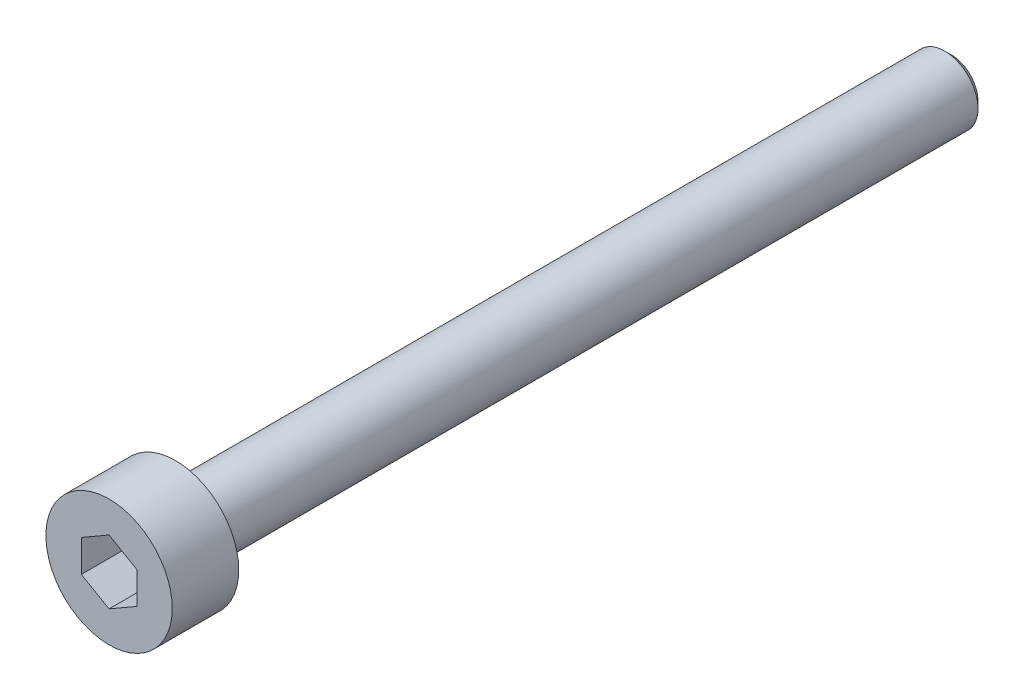
SolidWorks part; units mm, degrees
ref_plane "Front Plane" through (0, 0, 0) normal (0, 0, 1) x (1, 0, 0)
ref_plane "Top Plane" through (0, 0, 0) normal (0, 1, 0) x (1, 0, 0)
ref_plane "Right Plane" through (0, 0, 0) normal (1, 0, 0) x (0, 0, -1)
sketch "Sketch1" plane through (0, 0, 0) normal (0, 0, 1) x (1, 0, 0)
  circle A0 centre (0, 0) radius 2.85
  dimension "D1" = 5.7
extrude "Boss-Extrude1" add sketch "Sketch1" along normal blind 3
sketch "Sketch2" plane through (0, 0, 0) normal (0, 0, -1) x (-1, 0, 0)
  circle A0 centre (0, 0) radius 1.5
  dimension "D1" = 3
extrude "Boss-Extrude2" add sketch "Sketch2" along normal blind 35
chamfer "Chamfer1" distance 0.3 angle 45 1 edges at (-1.5, 0, -35)
sketch "Sketch3" plane through (0, 0, 3) normal (0, 0, 1) x (1, 0, 0)
  line L1 (0, 1.4434) -> (-1.25, 0.7217)
  line L2 (-1.25, 0.7217) -> (-1.25, -0.7217)
  line L3 (-1.25, -0.7217) -> (0, -1.4434)
  line L4 (0, -1.4434) -> (1.25, -0.7217)
  line L5 (1.25, -0.7217) -> (1.25, 0.7217)
  line L6 (1.25, 0.7217) -> (0, 1.4434)
  circle A0 centre (0, 0) radius 1.25 construction
  dimension "D1" = 2.5
extrude "Cut-Extrude1" cut sketch "Sketch3" against normal blind 2
